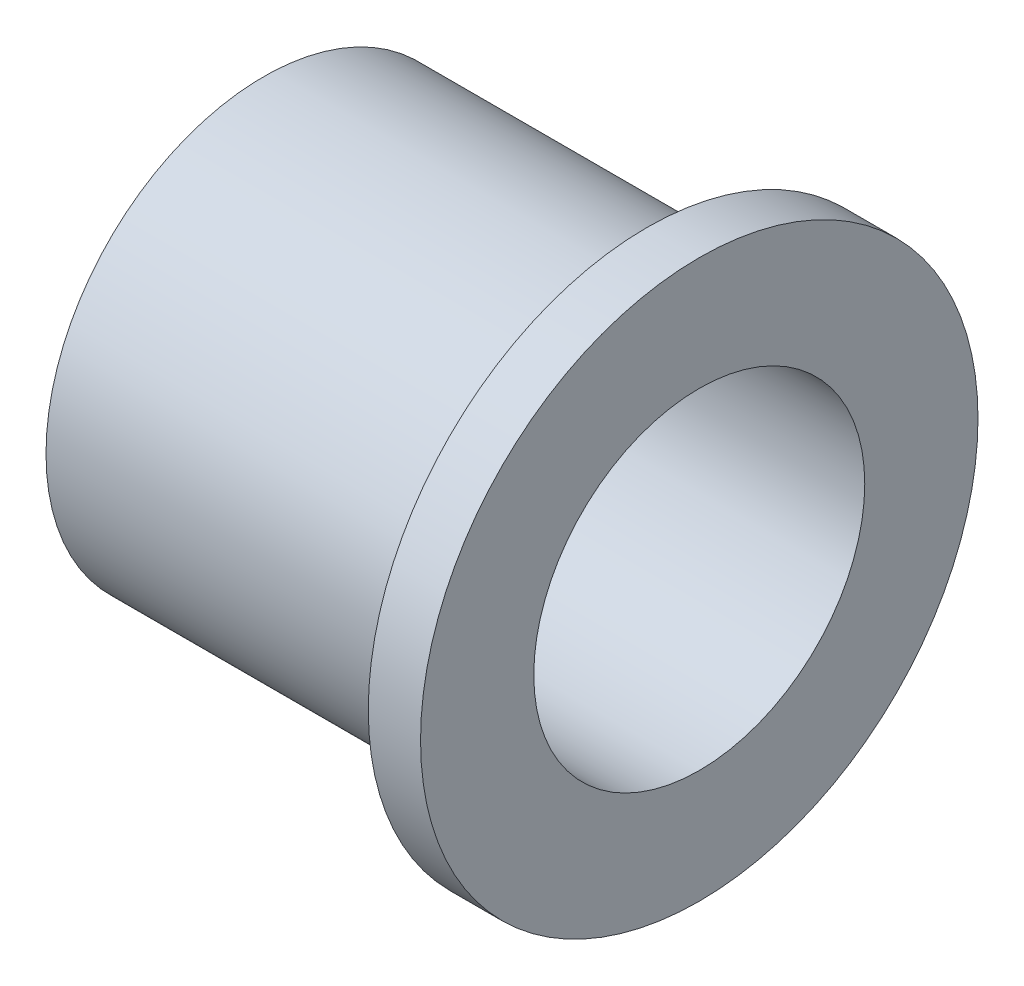
SolidWorks part; units mm, degrees
ref_plane "Plano frontal" through (0, 0, 0) normal (0, 0, 1) x (1, 0, 0)
ref_plane "Plano superior" through (0, 0, 0) normal (0, 1, 0) x (1, 0, 0)
ref_plane "Plano direito" through (0, 0, 0) normal (1, 0, 0) x (0, 0, -1)
sketch "Esboço1" plane through (0, 0, 0) normal (1, 0, 0) x (0, 0, -1)
  circle A0 centre (0, 0) radius 12.5
  dimension "D1" = 25
extrude "Ressalto-extrusão1" add sketch "Esboço1" along normal blind 22
sketch "Esboço2" plane through (22, 0, 0) normal (1, 0, 0) x (0, 0, -1)
  circle A0 centre (0, 0) radius 16
  dimension "D1" = 32
extrude "Ressalto-extrusão2" add sketch "Esboço2" along normal blind 3
sketch "Esboço3" plane through (25, 0, 0) normal (1, 0, 0) x (0, 0, -1)
  circle A0 centre (0, 0) radius 9.5
  dimension "D1" = 19
extrude "Corte-extrusão1" cut sketch "Esboço3" against normal through all
